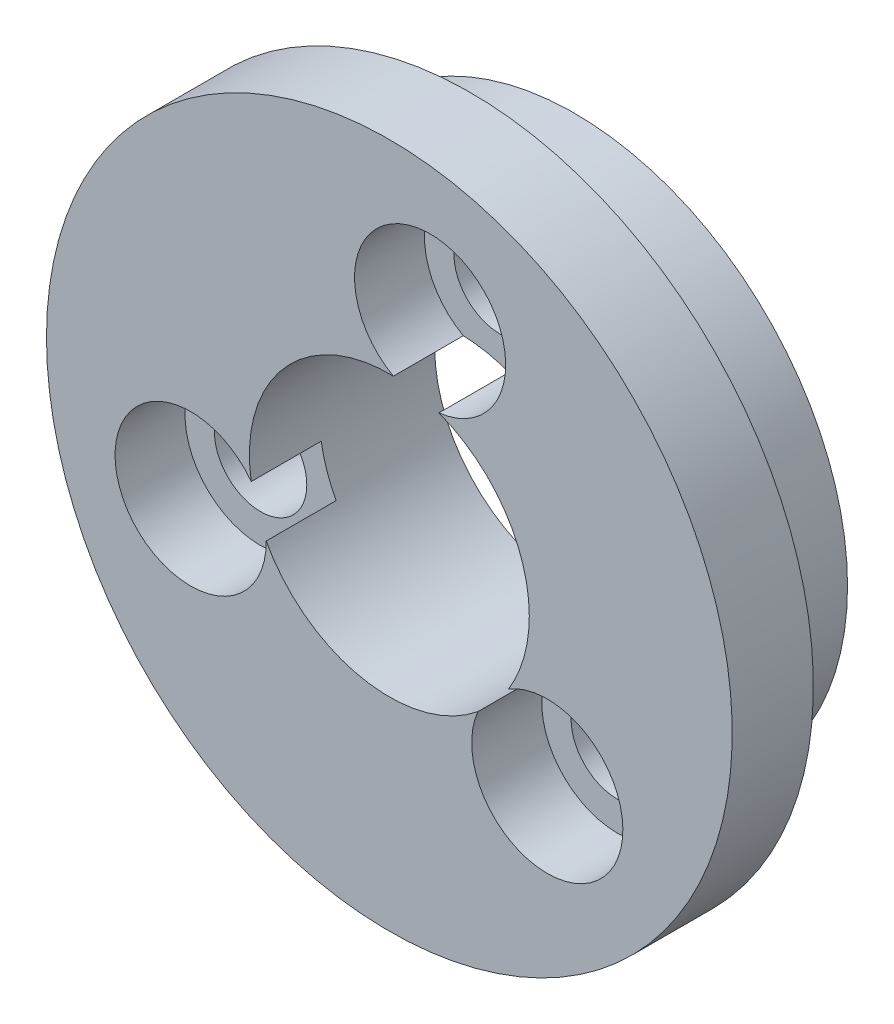
SolidWorks part; units mm, degrees
ref_plane "Front Plane" through (0, 0, 0) normal (0, 0, 1) x (1, 0, 0)
ref_plane "Top Plane" through (0, 0, 0) normal (0, 1, 0) x (1, 0, 0)
ref_plane "Right Plane" through (0, 0, 0) normal (1, 0, 0) x (0, 0, -1)
sketch "Sketch1" plane through (0, 0, 0) normal (0, 0, 1) x (1, 0, 0)
  circle A0 centre (350.15, -0.3675) radius 12.25
  dimension "D1" = 24.5
extrude "Boss-Extrude1" add sketch "Sketch1" along normal up to surface (2.9 mm away)
sketch "Sketch2" plane through (0, 0, 2.9) normal (0, 0, 1) x (1, 0, 0)
  circle A0 centre (350.15, -0.3675) radius 5
  dimension "D1" = 10
extrude "Cut-Extrude1" cut sketch "Sketch2" against normal up to next
sketch "Sketch5" plane through (0, 0, 2.9) normal (0, 0, 1) x (1, 0, 0)
  line L0 (340.6836, -3.5905) -> (352.092, 9.4421) construction
  line L1 (352.092, 9.4421) -> (357.6744, -6.9542) construction
  line L2 (357.6744, -6.9542) -> (340.6836, -3.5905) construction
  line L3 (350.15, -0.3675) -> (355.7933, -5.3075) construction
  line L6 (350.15, -0.3675) -> (343.0502, -2.7847) construction
  line L7 (350.15, -0.3675) -> (351.6065, 6.9897) construction
  circle A1 centre (350.15, -0.3675) radius 5 construction
  circle A3 centre (343.0502, -2.7847) radius 1.65
  circle A4 centre (355.7933, -5.3075) radius 1.65
  circle A5 centre (351.6065, 6.9897) radius 1.65
  dimension "D2" = 3.3
  dimension "D1" = 7.5
extrude "Cut-Extrude2" cut sketch "Sketch5" against normal up to next
sketch "Sketch6" plane through (0, 0, 0) normal (0, 0, -1) x (-1, 0, 0)
  circle A0 centre (-350.15, -0.3675) radius 9.75
  circle A3 centre (-350.15, -0.3675) radius 5
  dimension "D1" = 19.5
extrude "Boss-Extrude2" add sketch "Sketch6" along normal up to surface (3.72 mm away)
sketch "Sketch7" plane through (0, 0, 0) normal (0, 0, 1) x (1, 0, 0)
  circle A0 centre (351.6065, 6.9897) radius 1.65
  circle A1 centre (343.0502, -2.7847) radius 1.65
  circle A2 centre (355.7933, -5.3075) radius 1.65
extrude "Cut-Extrude3" cut sketch "Sketch7" against normal up to surface (3.72 mm away) up to face at (355.15, -0.3675, -3.72)
sketch "Sketch8" plane through (0, 0, 2.9) normal (0, 0, 1) x (1, 0, 0)
  circle A0 centre (351.6065, 6.9897) radius 2.7
  circle A1 centre (355.7933, -5.3075) radius 2.7
  circle A2 centre (343.0502, -2.7847) radius 2.7
  dimension "D1" = 5.4
extrude "Cut-Extrude4" cut sketch "Sketch8" against normal blind 2.5
